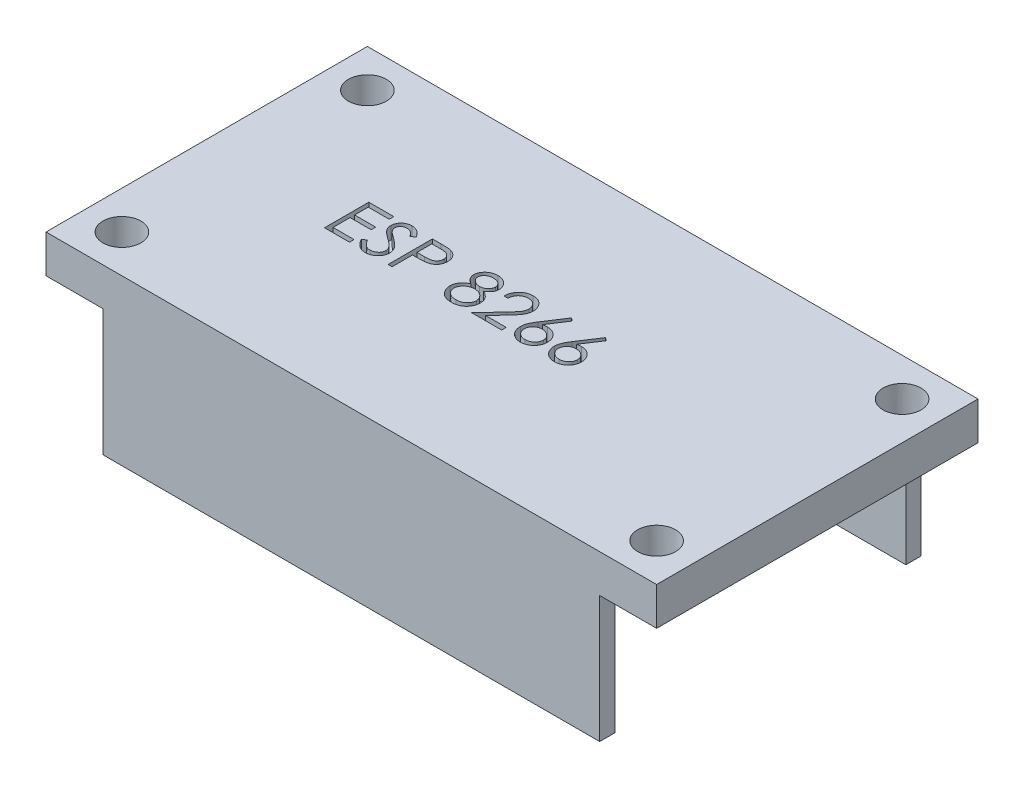
SolidWorks part; units mm, degrees
ref_plane "Front Plane" through (0, 0, 0) normal (0, 0, 1) x (1, 0, 0)
ref_plane "Top Plane" through (0, 0, 0) normal (0, 1, 0) x (1, 0, 0)
ref_plane "Right Plane" through (0, 0, 0) normal (1, 0, 0) x (0, 0, -1)
sketch "Sketch1" plane through (0, 0, 0) normal (0, 1, 0) x (1, 0, 0)
  line L1 (0, 0) -> (48.26, 0)
  line L2 (0, 0) -> (0, 25.4)
  line L3 (0, 25.4) -> (48.26, 25.4)
  line L4 (48.26, 0) -> (48.26, 25.4)
  dimension "D1" = 48.26
  dimension "D2" = 25.4
extrude "Boss-Extrude1" add sketch "Sketch1" along normal blind 13
sketch "Sketch2" plane through (0, 0, 0) normal (0, -1, 0) x (1, 0, 0)
  line L0 (0, -25.4) -> (0, 0) construction
  line L2 (0, -1.2) -> (0, -24.2)
  line L4 (48.26, -1.2) -> (48.26, -24.2)
  line L5 (48.26, 0) -> (48.26, -25.4) construction
  line L7 (0, 0) -> (48.26, 0) construction
  line L9 (43.76, -1.2) -> (43.76, 0)
  line L10 (43.76, 0) -> (48.26, 0)
  line L11 (48.26, -1.2) -> (48.26, 0)
  line L12 (4.5, -1.2) -> (43.76, -1.2)
  line L14 (0, -1.2) -> (0, 0)
  line L15 (0, 0) -> (4.5, 0)
  line L16 (4.5, -1.2) -> (4.5, 0)
  line L17 (0, -25.4) -> (4.5, -25.4)
  line L18 (0, -25.4) -> (0, -24.2)
  line L20 (4.5, -25.4) -> (4.5, -24.2)
  line L21 (48.26, -25.4) -> (43.76, -25.4)
  line L22 (48.26, -25.4) -> (48.26, -24.2)
  line L24 (43.76, -25.4) -> (43.76, -24.2)
  line L25 (43.76, -24.2) -> (4.5, -24.2)
  dimension "D1" = 23
  dimension "D3" = 4.5
  dimension "D4" = 4.5
  dimension "D5" = 4.5
  dimension "D6" = 4.5
extrude "Cut-Extrude1" cut sketch "Sketch2" against normal blind 10
sketch "Sketch3" plane through (0, 13, 0) normal (0, 1, 0) x (1, 0, 0)
  text T0 "ESP 8266"
extrude "Cut-Extrude2" cut sketch "Sketch3" against normal blind 1
sketch "Sketch4" plane through (0, 13, 0) normal (0, 1, 0) x (1, 0, 0)
  line L0 (0, 0) -> (48.26, 0) construction
  line L1 (0, 25.4) -> (0, 0) construction
  line L2 (48.26, 25.4) -> (0, 25.4) construction
  circle A0 centre (3, 3) radius 1.5
  circle A1 centre (3, 22.4) radius 1.5
  circle A4 centre (45.26, 3) radius 1.5
  circle A5 centre (45.26, 22.4) radius 1.5
  dimension "D1" = 3
  dimension "D2" = 3
  dimension "D3" = 3
  dimension "D4" = 3
  dimension "D5" = 3
  dimension "D6" = 3
extrude "Cut-Extrude3" cut sketch "Sketch4" against normal blind 30
